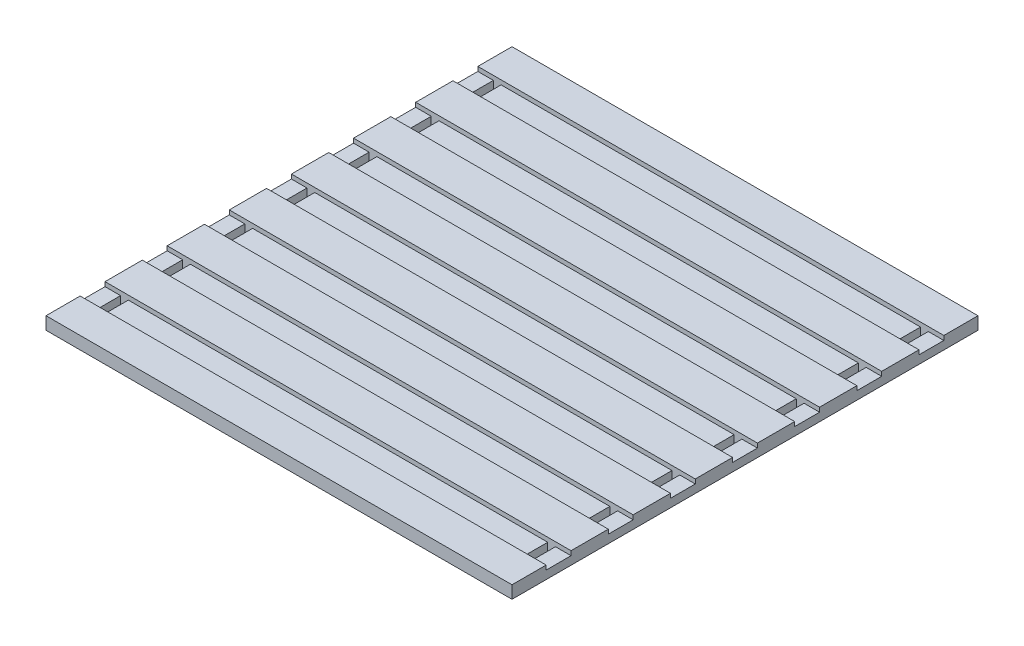
SolidWorks part; units mm, degrees
material "Maple"
ref_plane "Front Plane" through (0, 0, 0) normal (0, 0, 1) x (1, 0, 0)
ref_plane "Top Plane" through (0, 0, 0) normal (0, 1, 0) x (1, 0, 0)
ref_plane "Right Plane" through (0, 0, 0) normal (1, 0, 0) x (0, 0, -1)
sketch "Sketch1" plane through (0, 0, 0) normal (0, 1, 0) x (1, 0, 0)
  line L0 (-95.25, 95.25) -> (95.25, -95.25) construction
  line L1 (-95.25, 95.25) -> (95.25, 95.25)
  line L2 (-95.25, 95.25) -> (-95.25, -95.25)
  line L3 (-95.25, -95.25) -> (95.25, -95.25)
  line L4 (95.25, 95.25) -> (95.25, -95.25)
  dimension "D1" = 190.5
extrude "Boss-Extrude1" add sketch "Sketch1" along normal blind 5.1594
sketch "Sketch2" plane through (0, 5.1594, 0) normal (0, 1, 0) x (1, 0, 0)
  line L0 (-95.25, 95.25) -> (-95.25, -95.25) construction
  line L1 (-95.25, 81.28) -> (95.25, 81.28)
  line L2 (-95.25, 81.28) -> (-95.25, 71.12)
  line L3 (-95.25, 71.12) -> (95.25, 71.12)
  line L4 (95.25, 81.28) -> (95.25, 71.12)
  line L6 (-95.25, 76.2) -> (95.25, 76.2) construction
  line L7 (95.25, 95.25) -> (-95.25, 95.25) construction
  line L8 (-95.25, 55.88) -> (95.25, 55.88)
  line L9 (-95.25, 55.88) -> (-95.25, 45.72)
  line L10 (-95.25, 45.72) -> (95.25, 45.72)
  line L11 (95.25, 55.88) -> (95.25, 45.72)
  line L12 (-95.25, 30.48) -> (95.25, 30.48)
  line L13 (-95.25, 30.48) -> (-95.25, 20.32)
  line L14 (-95.25, 20.32) -> (95.25, 20.32)
  line L15 (95.25, 30.48) -> (95.25, 20.32)
  line L16 (-95.25, 5.08) -> (95.25, 5.08)
  line L17 (-95.25, 5.08) -> (-95.25, -5.08)
  line L18 (-95.25, -5.08) -> (95.25, -5.08)
  line L19 (95.25, 5.08) -> (95.25, -5.08)
  line L20 (-95.25, -20.32) -> (95.25, -20.32)
  line L21 (-95.25, -20.32) -> (-95.25, -30.48)
  line L22 (-95.25, -30.48) -> (95.25, -30.48)
  line L23 (95.25, -20.32) -> (95.25, -30.48)
  line L24 (-95.25, -45.72) -> (95.25, -45.72)
  line L25 (-95.25, -45.72) -> (-95.25, -55.88)
  line L26 (-95.25, -55.88) -> (95.25, -55.88)
  line L27 (95.25, -45.72) -> (95.25, -55.88)
  line L28 (-95.25, -71.12) -> (95.25, -71.12)
  line L29 (-95.25, -71.12) -> (-95.25, -81.28)
  line L30 (-95.25, -81.28) -> (95.25, -81.28)
  line L31 (95.25, -71.12) -> (95.25, -81.28)
  dimension "D1" = 10.16
  dimension "D2" = 190.5
  dimension "D3" = 19.05
  dimension "D4" = 7
extrude "Cut-Extrude1" cut sketch "Sketch2" against normal blind 1.778
sketch "Sketch3" plane through (0, 3.3814, 0) normal (0, 1, 0) x (1, 0, 0)
  line L0 (95.25, 81.28) -> (-95.25, 81.28) construction
  line L1 (-88.9, 81.28) -> (-85.725, 81.28)
  line L2 (-88.9, 81.28) -> (-88.9, 71.12)
  line L3 (-88.9, 71.12) -> (-85.725, 71.12)
  line L4 (-85.725, 81.28) -> (-85.725, 71.12)
  line L5 (-95.25, 71.12) -> (95.25, 71.12) construction
  line L6 (-95.25, 81.28) -> (-95.25, 71.12) construction
  line L7 (0, 95.25) -> (0, -95.25) construction
  line L8 (95.25, 95.25) -> (-95.25, 95.25) construction
  line L9 (-95.25, -95.25) -> (95.25, -95.25) construction
  line L10 (88.9, 81.28) -> (88.9, 71.12)
  line L11 (88.9, 71.12) -> (85.725, 71.12)
  line L12 (85.725, 81.28) -> (85.725, 71.12)
  line L13 (88.9, 81.28) -> (85.725, 81.28)
  dimension "D1" = 3.175
  dimension "D2" = 6.35
extrude "Cut-Extrude3" cut sketch "Sketch3" against normal through all
pattern_linear "LPattern1" count 7 spacing 25.4 along (0, 0, 1) of "Cut-Extrude3"
